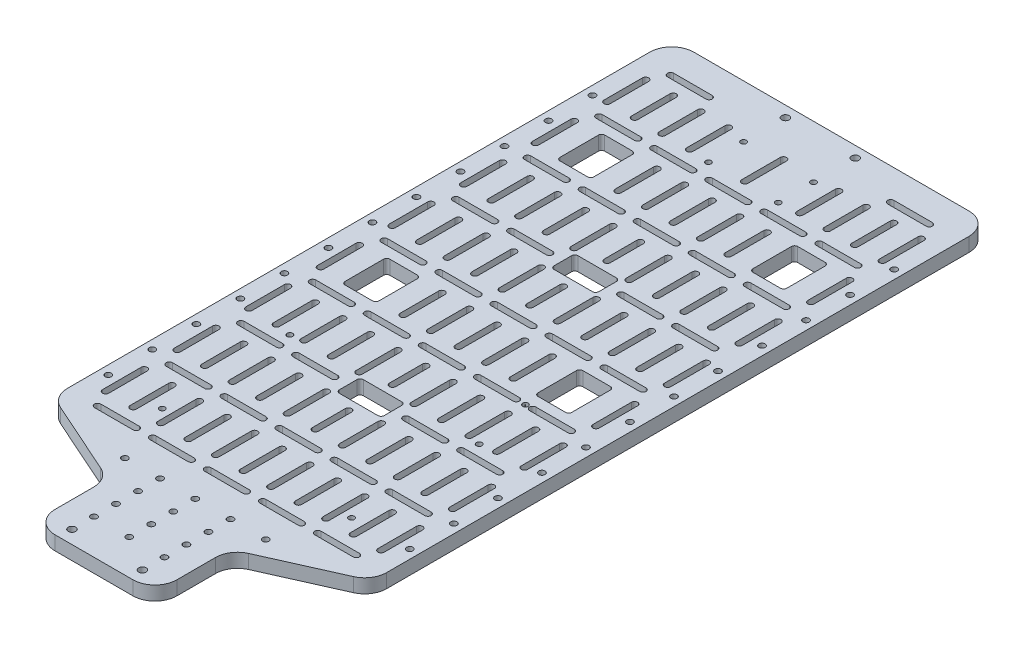
SolidWorks part; units mm, degrees
ref_plane "Front Plane" through (0, 0, 0) normal (0, 0, 1) x (1, 0, 0)
ref_plane "Top Plane" through (0, 0, 0) normal (0, 1, 0) x (1, 0, 0)
ref_plane "Right Plane" through (0, 0, 0) normal (1, 0, 0) x (0, 0, -1)
sketch "Sketch1" plane through (0, 0, 0) normal (0, 1, 0) x (1, 0, 0)
  line L0 (-72.5, 0) -> (72.5, 0)
  line L1 (-72.5, 0) -> (-72.5, -335)
  line L2 (72.5, 0) -> (72.5, -335)
  line L3 (72.5, -335) -> (-72.5, -335)
  line L4 (0, 0) -> (0, -335) construction
  dimension "D1" = 145
  dimension "D2" = 335
extrude "Boss-Extrude1" add sketch "Sketch1" along normal blind 6.35
sketch "Sketch2" plane through (0, 6.35, 0) normal (0, 1, 0) x (1, 0, 0)
  line L0 (72.5, 0) -> (-72.5, 0) construction
  line L1 (-72.5, -335) -> (72.5, -335) construction
  line L2 (0, 0) -> (0, -335) construction
  line L3 (-27.685, -301) -> (-72.5, -281)
  line L4 (16.25, -273.1552) -> (33.75, -273.1552)
  line L5 (-27.685, -335) -> (-27.685, -301)
  line L6 (-72.5, 0) -> (-72.5, -335) construction
  line L7 (-72.5, -281) -> (-72.5, -335)
  line L8 (-72.5, -335) -> (-27.685, -335)
  line L9 (-8.75, -273.1552) -> (8.75, -273.1552)
  line L10 (8.75, -276) -> (-8.75, -276)
  line L11 (33.75, -276) -> (16.25, -276)
  line L12 (41.25, -273.1552) -> (58.75, -273.1552)
  line L13 (58.75, -276) -> (41.25, -276)
  line L14 (-33.75, -273.1552) -> (-16.25, -273.1552)
  line L15 (-16.25, -276) -> (-33.75, -276)
  line L16 (-58.75, -273.1552) -> (-41.25, -273.1552)
  line L17 (-41.25, -276) -> (-58.75, -276)
  line L20 (-1.4224, -249.5776) -> (-1.4224, -267.0776)
  line L21 (1.4224, -249.5776) -> (1.4224, -267.0776)
  line L22 (13.9224, -249.5776) -> (13.9224, -267.0776)
  line L23 (11.0776, -249.5776) -> (11.0776, -267.0776)
  line L24 (26.4224, -249.5776) -> (26.4224, -267.0776)
  line L25 (23.5776, -249.5776) -> (23.5776, -267.0776)
  line L26 (38.9224, -249.5776) -> (38.9224, -267.0776)
  line L27 (36.0776, -249.5776) -> (36.0776, -267.0776)
  line L28 (51.4224, -249.5776) -> (51.4224, -267.0776)
  line L29 (48.5776, -249.5776) -> (48.5776, -267.0776)
  line L30 (63.9224, -249.5776) -> (63.9224, -267.0776)
  line L31 (61.0776, -249.5776) -> (61.0776, -267.0776)
  line L32 (-11.1007, -249.5776) -> (-11.1007, -267.0776)
  line L33 (-13.9455, -249.5776) -> (-13.9455, -267.0776)
  line L34 (-23.6238, -249.5776) -> (-23.6238, -267.0776)
  line L35 (-26.4686, -249.5776) -> (-26.4686, -267.0776)
  line L36 (-36.1468, -249.5776) -> (-36.1468, -267.0776)
  line L37 (-38.9916, -249.5776) -> (-38.9916, -267.0776)
  line L38 (-48.6699, -249.5776) -> (-48.6699, -267.0776)
  line L39 (-51.5147, -249.5776) -> (-51.5147, -267.0776)
  line L40 (-61.193, -249.5776) -> (-61.193, -267.0776)
  line L41 (-64.0378, -249.5776) -> (-64.0378, -267.0776)
  line L42 (-58.75, -240.6065) -> (-41.25, -240.6065)
  line L43 (-41.25, -243.4513) -> (-58.75, -243.4513)
  line L44 (-61.193, -217.0289) -> (-61.193, -234.5289)
  line L45 (-64.0378, -217.0289) -> (-64.0378, -234.5289)
  line L46 (-48.6699, -217.0289) -> (-48.6699, -234.5289)
  line L47 (-51.5147, -217.0289) -> (-51.5147, -234.5289)
  line L48 (-36.1468, -217.0289) -> (-36.1468, -234.5289)
  line L49 (-38.9916, -217.0289) -> (-38.9916, -234.5289)
  line L50 (-23.6238, -217.0289) -> (-23.6238, -234.5289)
  line L51 (-26.4686, -217.0289) -> (-26.4686, -234.5289)
  line L52 (-11.1007, -217.0289) -> (-11.1007, -234.5289)
  line L53 (-13.9455, -217.0289) -> (-13.9455, -234.5289)
  line L54 (-33.75, -240.6065) -> (-16.25, -240.6065)
  line L55 (-16.25, -243.4513) -> (-33.75, -243.4513)
  line L58 (13.9224, -217.0289) -> (13.9224, -234.5289)
  line L59 (11.0776, -217.0289) -> (11.0776, -234.5289)
  line L60 (26.4224, -217.0289) -> (26.4224, -234.5289)
  line L61 (23.5776, -217.0289) -> (23.5776, -234.5289)
  line L62 (16.25, -240.6065) -> (33.75, -240.6065)
  line L63 (33.75, -243.4513) -> (16.25, -243.4513)
  line L64 (-8.75, -240.6065) -> (8.75, -240.6065)
  line L65 (8.75, -243.4513) -> (-8.75, -243.4513)
  line L66 (38.9224, -217.0289) -> (38.9224, -234.5289)
  line L67 (36.0776, -217.0289) -> (36.0776, -234.5289)
  line L68 (51.4224, -217.0289) -> (51.4224, -234.5289)
  line L69 (48.5776, -217.0289) -> (48.5776, -234.5289)
  line L70 (41.25, -240.6065) -> (58.75, -240.6065)
  line L71 (58.75, -243.4513) -> (41.25, -243.4513)
  line L72 (63.9224, -217.0289) -> (63.9224, -234.5289)
  line L73 (61.0776, -217.0289) -> (61.0776, -234.5289)
  line L74 (-58.75, -208.0578) -> (-41.25, -208.0578)
  line L75 (-41.25, -210.9026) -> (-58.75, -210.9026)
  line L76 (-61.193, -184.4802) -> (-61.193, -201.9802)
  line L77 (-64.0378, -184.4802) -> (-64.0378, -201.9802)
  line L78 (-48.6699, -184.4802) -> (-48.6699, -201.9802)
  line L79 (-51.5147, -184.4802) -> (-51.5147, -201.9802)
  line L80 (-36.1468, -184.4802) -> (-36.1468, -201.9802)
  line L81 (-38.9916, -184.4802) -> (-38.9916, -201.9802)
  line L82 (-23.6238, -184.4802) -> (-23.6238, -201.9802)
  line L83 (-26.4686, -184.4802) -> (-26.4686, -201.9802)
  line L84 (-11.1007, -184.4802) -> (-11.1007, -201.9802)
  line L85 (-13.9455, -184.4802) -> (-13.9455, -201.9802)
  line L86 (-33.75, -208.0578) -> (-16.25, -208.0578)
  line L87 (-16.25, -210.9026) -> (-33.75, -210.9026)
  line L90 (13.9224, -184.4802) -> (13.9224, -201.9802)
  line L91 (11.0776, -184.4802) -> (11.0776, -201.9802)
  line L92 (26.4224, -184.4802) -> (26.4224, -201.9802)
  line L93 (23.5776, -184.4802) -> (23.5776, -201.9802)
  line L94 (16.25, -208.0578) -> (33.75, -208.0578)
  line L95 (33.75, -210.9026) -> (16.25, -210.9026)
  line L98 (38.9224, -184.4802) -> (38.9224, -201.9802)
  line L99 (36.0776, -184.4802) -> (36.0776, -201.9802)
  line L100 (51.4224, -184.4802) -> (51.4224, -201.9802)
  line L101 (48.5776, -184.4802) -> (48.5776, -201.9802)
  line L102 (41.25, -208.0578) -> (58.75, -208.0578)
  line L103 (58.75, -210.9026) -> (41.25, -210.9026)
  line L104 (63.9224, -184.4802) -> (63.9224, -201.9802)
  line L105 (61.0776, -184.4802) -> (61.0776, -201.9802)
  line L106 (-58.75, -175.509) -> (-41.25, -175.509)
  line L107 (-41.25, -178.3538) -> (-58.75, -178.3538)
  line L108 (-61.193, -151.9314) -> (-61.193, -169.4314)
  line L109 (-64.0378, -151.9314) -> (-64.0378, -169.4314)
  line L111 (-51.5147, -151.9314) -> (-51.5147, -169.4314)
  line L112 (-36.1468, -151.9314) -> (-36.1468, -169.4314)
  line L114 (-23.6238, -151.9314) -> (-23.6238, -169.4314)
  line L115 (-26.4686, -151.9314) -> (-26.4686, -169.4314)
  line L116 (-11.1007, -151.9314) -> (-11.1007, -169.4314)
  line L117 (-13.9455, -151.9314) -> (-13.9455, -169.4314)
  line L118 (-33.75, -175.509) -> (-16.25, -175.509)
  line L119 (-16.25, -178.3538) -> (-33.75, -178.3538)
  line L120 (1.4224, -151.9314) -> (1.4224, -169.4314)
  line L121 (-1.4224, -151.9314) -> (-1.4224, -169.4314)
  line L122 (13.9224, -151.9314) -> (13.9224, -169.4314)
  line L123 (11.0776, -151.9314) -> (11.0776, -169.4314)
  line L124 (26.4224, -151.9314) -> (26.4224, -169.4314)
  line L125 (23.5776, -151.9314) -> (23.5776, -169.4314)
  line L126 (16.25, -175.509) -> (33.75, -175.509)
  line L127 (33.75, -178.3538) -> (16.25, -178.3538)
  line L128 (-8.75, -175.509) -> (8.75, -175.509)
  line L129 (8.75, -178.3538) -> (-8.75, -178.3538)
  line L134 (41.25, -175.509) -> (58.75, -175.509)
  line L135 (58.75, -178.3538) -> (41.25, -178.3538)
  line L136 (63.9224, -151.9314) -> (63.9224, -169.4314)
  line L137 (61.0776, -151.9314) -> (61.0776, -169.4314)
  line L138 (-58.75, -142.9603) -> (-41.25, -142.9603)
  line L139 (-41.25, -145.8051) -> (-58.75, -145.8051)
  line L140 (-61.193, -119.3827) -> (-61.193, -136.8827)
  line L141 (-64.0378, -119.3827) -> (-64.0378, -136.8827)
  line L142 (-48.6699, -119.3827) -> (-48.6699, -136.8827)
  line L143 (-51.5147, -119.3827) -> (-51.5147, -136.8827)
  line L144 (-36.1468, -119.3827) -> (-36.1468, -136.8827)
  line L145 (-38.9916, -119.3827) -> (-38.9916, -136.8827)
  line L146 (-23.6238, -119.3827) -> (-23.6238, -136.8827)
  line L147 (-26.4686, -119.3827) -> (-26.4686, -136.8827)
  line L148 (-11.1007, -119.3827) -> (-11.1007, -136.8827)
  line L149 (-13.9455, -119.3827) -> (-13.9455, -136.8827)
  line L150 (-33.75, -142.9603) -> (-16.25, -142.9603)
  line L151 (-16.25, -145.8051) -> (-33.75, -145.8051)
  line L154 (13.9224, -119.3827) -> (13.9224, -136.8827)
  line L155 (11.0776, -119.3827) -> (11.0776, -136.8827)
  line L156 (26.4224, -119.3827) -> (26.4224, -136.8827)
  line L157 (23.5776, -119.3827) -> (23.5776, -136.8827)
  line L158 (16.25, -142.9603) -> (33.75, -142.9603)
  line L159 (33.75, -145.8051) -> (16.25, -145.8051)
  line L160 (-8.75, -142.9603) -> (8.75, -142.9603)
  line L161 (8.75, -145.8051) -> (-8.75, -145.8051)
  line L162 (38.9224, -119.3827) -> (38.9224, -136.8827)
  line L163 (36.0776, -119.3827) -> (36.0776, -136.8827)
  line L164 (51.4224, -119.3827) -> (51.4224, -136.8827)
  line L165 (48.5776, -119.3827) -> (48.5776, -136.8827)
  line L166 (41.25, -142.9603) -> (58.75, -142.9603)
  line L167 (58.75, -145.8051) -> (41.25, -145.8051)
  line L168 (63.9224, -119.3827) -> (63.9224, -136.8827)
  line L169 (61.0776, -119.3827) -> (61.0776, -136.8827)
  line L170 (-58.75, -110.4116) -> (-41.25, -110.4116)
  line L171 (-41.25, -113.2564) -> (-58.75, -113.2564)
  line L172 (-61.193, -86.834) -> (-61.193, -104.334)
  line L173 (-64.0378, -86.834) -> (-64.0378, -104.334)
  line L174 (-48.6699, -86.834) -> (-48.6699, -104.334)
  line L175 (-51.5147, -86.834) -> (-51.5147, -104.334)
  line L176 (-36.1468, -86.834) -> (-36.1468, -104.334)
  line L177 (-38.9916, -86.834) -> (-38.9916, -104.334)
  line L178 (-23.6238, -86.834) -> (-23.6238, -104.334)
  line L179 (-26.4686, -86.834) -> (-26.4686, -104.334)
  line L180 (-11.1007, -86.834) -> (-11.1007, -104.334)
  line L181 (-13.9455, -86.834) -> (-13.9455, -104.334)
  line L182 (-33.75, -110.4116) -> (-16.25, -110.4116)
  line L183 (-16.25, -113.2564) -> (-33.75, -113.2564)
  line L186 (13.9224, -86.834) -> (13.9224, -104.334)
  line L187 (11.0776, -86.834) -> (11.0776, -104.334)
  line L188 (26.4224, -86.834) -> (26.4224, -104.334)
  line L189 (23.5776, -86.834) -> (23.5776, -104.334)
  line L190 (16.25, -110.4116) -> (33.75, -110.4116)
  line L191 (33.75, -113.2564) -> (16.25, -113.2564)
  line L194 (38.9224, -86.834) -> (38.9224, -104.334)
  line L195 (36.0776, -86.834) -> (36.0776, -104.334)
  line L196 (51.4224, -86.834) -> (51.4224, -104.334)
  line L197 (48.5776, -86.834) -> (48.5776, -104.334)
  line L198 (41.25, -110.4116) -> (58.75, -110.4116)
  line L199 (58.75, -113.2564) -> (41.25, -113.2564)
  line L200 (63.9224, -86.834) -> (63.9224, -104.334)
  line L201 (61.0776, -86.834) -> (61.0776, -104.334)
  line L202 (-58.75, -77.8629) -> (-41.25, -77.8629)
  line L203 (-41.25, -80.7077) -> (-58.75, -80.7077)
  line L204 (-61.193, -54.2853) -> (-61.193, -71.7853)
  line L205 (-64.0378, -54.2853) -> (-64.0378, -71.7853)
  line L207 (-51.5147, -54.2853) -> (-51.5147, -71.7853)
  line L208 (-36.1468, -54.2853) -> (-36.1468, -71.7853)
  line L210 (-23.6238, -54.2853) -> (-23.6238, -71.7853)
  line L211 (-26.4686, -54.2853) -> (-26.4686, -71.7853)
  line L212 (-11.1007, -54.2853) -> (-11.1007, -71.7853)
  line L213 (-13.9455, -54.2853) -> (-13.9455, -71.7853)
  line L214 (-33.75, -77.8629) -> (-16.25, -77.8629)
  line L215 (-16.25, -80.7077) -> (-33.75, -80.7077)
  line L216 (1.4224, -54.2853) -> (1.4224, -71.7853)
  line L217 (-1.4224, -54.2853) -> (-1.4224, -71.7853)
  line L218 (13.9224, -54.2853) -> (13.9224, -71.7853)
  line L219 (11.0776, -54.2853) -> (11.0776, -71.7853)
  line L220 (26.4224, -54.2853) -> (26.4224, -71.7853)
  line L221 (23.5776, -54.2853) -> (23.5776, -71.7853)
  line L222 (16.25, -77.8629) -> (33.75, -77.8629)
  line L223 (33.75, -80.7077) -> (16.25, -80.7077)
  line L224 (-8.75, -77.8629) -> (8.75, -77.8629)
  line L225 (8.75, -80.7077) -> (-8.75, -80.7077)
  line L230 (41.25, -77.8629) -> (58.75, -77.8629)
  line L231 (58.75, -80.7077) -> (41.25, -80.7077)
  line L232 (63.9224, -54.2853) -> (63.9224, -71.7853)
  line L233 (61.0776, -54.2853) -> (61.0776, -71.7853)
  line L234 (-41.25, -48.2077) -> (-58.75, -48.2077)
  line L235 (-58.75, -45.3629) -> (-41.25, -45.3629)
  line L236 (-33.75, -45.3629) -> (-16.25, -45.3629)
  line L237 (-16.25, -48.2077) -> (-33.75, -48.2077)
  line L238 (-8.75, -45.3629) -> (8.75, -45.3629)
  line L239 (8.75, -48.2077) -> (-8.75, -48.2077)
  line L240 (16.25, -45.3629) -> (33.75, -45.3629)
  line L241 (33.75, -48.2077) -> (16.25, -48.2077)
  line L242 (41.25, -45.3629) -> (58.75, -45.3629)
  line L243 (58.75, -48.2077) -> (41.25, -48.2077)
  line L244 (72.5, -281) -> (72.5, -335)
  line L245 (27.685, -301) -> (72.5, -281)
  line L246 (27.685, -335) -> (27.685, -301)
  line L247 (72.5, -335) -> (27.685, -335)
  line L248 (-48.6699, -21.7853) -> (-48.6699, -39.2853)
  line L249 (-51.5147, -21.7853) -> (-51.5147, -39.2853)
  line L250 (-36.1468, -21.7853) -> (-36.1468, -39.2853)
  line L251 (-38.9916, -21.7853) -> (-38.9916, -39.2853)
  line L252 (51.4224, -21.7853) -> (51.4224, -39.2853)
  line L253 (48.5776, -21.7853) -> (48.5776, -39.2853)
  line L254 (38.9224, -21.7853) -> (38.9224, -39.2853)
  line L255 (36.0776, -21.7853) -> (36.0776, -39.2853)
  line L256 (63.9224, -21.7853) -> (63.9224, -39.2853)
  line L257 (61.0776, -21.7853) -> (61.0776, -39.2853)
  line L258 (-61.193, -21.7853) -> (-61.193, -39.2853)
  line L259 (-64.0378, -21.7853) -> (-64.0378, -39.2853)
  line L260 (-23.6238, -21.7853) -> (-23.6238, -39.2853)
  line L261 (-26.4686, -21.7853) -> (-26.4686, -39.2853)
  line L262 (26.4224, -21.7853) -> (26.4224, -39.2853)
  line L263 (23.5776, -21.7853) -> (23.5776, -39.2853)
  line L264 (1.4224, -21.7853) -> (1.4224, -39.2853)
  line L265 (-1.4224, -21.7853) -> (-1.4224, -39.2853)
  line L266 (-41.25, -15.7077) -> (-58.75, -15.7077)
  line L267 (-58.75, -12.8629) -> (-41.25, -12.8629)
  line L268 (41.25, -12.8629) -> (58.75, -12.8629)
  line L269 (58.75, -15.7077) -> (41.25, -15.7077)
  line L270 (-50.0923, -150.509) -> (-37.5692, -150.509)
  line L271 (-50.0923, -170.8538) -> (-37.5692, -170.8538)
  line L272 (-50.0923, -52.8629) -> (-37.5692, -52.8629)
  line L273 (-48.6699, -151.9314) -> (-48.6699, -169.4314) [skipped]
  line L274 (-38.9916, -151.9314) -> (-38.9916, -169.4314) [skipped]
  line L275 (38.9224, -151.9314) -> (38.9224, -169.4314) [skipped]
  line L276 (36.0776, -151.9314) -> (36.0776, -169.4314) [skipped]
  line L277 (51.4224, -151.9314) -> (51.4224, -169.4314) [skipped]
  line L278 (48.5776, -151.9314) -> (48.5776, -169.4314) [skipped]
  line L279 (-50.0923, -73.2077) -> (-37.5692, -73.2077)
  line L281 (-48.6699, -54.2853) -> (-48.6699, -71.7853) [skipped]
  line L282 (-38.9916, -54.2853) -> (-38.9916, -71.7853) [skipped]
  line L283 (38.9224, -54.2853) -> (38.9224, -71.7853) [skipped]
  line L284 (36.0776, -54.2853) -> (36.0776, -71.7853) [skipped]
  line L285 (51.4224, -54.2853) -> (51.4224, -71.7853) [skipped]
  line L286 (48.5776, -54.2853) -> (48.5776, -71.7853) [skipped]
  line L287 (8.75, -117.2564) -> (-8.75, -117.2564)
  line L288 (-8.75, -106.4116) -> (8.75, -106.4116)
  line L290 (-10.1724, -107.834) -> (-10.1724, -115.834)
  line L291 (10.1724, -107.834) -> (10.1724, -115.834)
  line L292 (8.75, -113.2564) -> (0, -113.2564) [skipped]
  line L293 (0, -110.4116) -> (8.75, -110.4116) [skipped]
  line L294 (1.4224, -86.8342) -> (1.42, -101.8342)
  line L295 (-1.4224, -86.8342) -> (-1.42, -101.8342)
  line L296 (1.4224, -86.834) -> (1.4224, -104.334) [skipped]
  line L297 (-1.4224, -86.834) -> (-1.4224, -104.334) [skipped]
  line L298 (1.4224, -121.8829) -> (1.42, -136.8829)
  line L299 (-1.4224, -121.8829) -> (-1.42, -136.8829)
  line L300 (1.4224, -119.3827) -> (1.4224, -136.8827) [skipped]
  line L301 (-1.4224, -119.3827) -> (-1.4224, -136.8827) [skipped]
  line L302 (8.75, -214.7564) -> (-8.75, -214.7564)
  line L303 (10.1724, -205.334) -> (10.1724, -213.334)
  line L304 (-8.75, -203.9116) -> (8.75, -203.9116)
  line L305 (-10.1724, -205.334) -> (-10.1724, -213.334)
  line L306 (1.4224, -184.3342) -> (1.42, -199.3342)
  line L307 (-1.4224, -184.3342) -> (-1.42, -199.3342)
  line L308 (1.4224, -219.3829) -> (1.42, -234.3829)
  line L309 (-1.4224, -219.3829) -> (-1.42, -234.3829)
  line L310 (1.4224, -184.4802) -> (1.4224, -201.9802) [skipped]
  line L311 (-1.4224, -184.4802) -> (-1.4224, -201.9802) [skipped]
  line L312 (-8.75, -208.0578) -> (8.75, -208.0578) [skipped]
  line L313 (8.75, -210.9026) -> (-8.75, -210.9026) [skipped]
  line L314 (1.4224, -217.0289) -> (1.4224, -234.5289) [skipped]
  line L315 (-1.4224, -217.0289) -> (-1.4224, -234.5289) [skipped]
  line L316 (50.0923, -52.8629) -> (37.5692, -52.8629)
  line L317 (36.1468, -54.2853) -> (36.1468, -71.7853)
  line L318 (50.0923, -73.2077) -> (37.5692, -73.2077)
  line L319 (51.5147, -54.2853) -> (51.5147, -71.7853)
  line L320 (50.0923, -150.509) -> (37.5692, -150.509)
  line L321 (36.1468, -151.9314) -> (36.1468, -169.4314)
  line L322 (50.0923, -170.8538) -> (37.5692, -170.8538)
  line L323 (51.5147, -151.9314) -> (51.5147, -169.4314)
  circle A0 centre (-15.875, -5) radius 1.7
  circle A1 centre (-16, -329) radius 1.7
  arc A2 (8.75, -276) -> (8.75, -273.1552) centre (8.75, -274.5776) ccw
  arc A3 (-8.75, -273.1552) -> (-8.75, -276) centre (-8.75, -274.5776) ccw
  arc A4 (33.75, -276) -> (33.75, -273.1552) centre (33.75, -274.5776) ccw
  arc A5 (16.25, -273.1552) -> (16.25, -276) centre (16.25, -274.5776) ccw
  arc A6 (58.75, -276) -> (58.75, -273.1552) centre (58.75, -274.5776) ccw
  arc A7 (41.25, -273.1552) -> (41.25, -276) centre (41.25, -274.5776) ccw
  arc A8 (-16.25, -276) -> (-16.25, -273.1552) centre (-16.25, -274.5776) ccw
  arc A9 (-33.75, -273.1552) -> (-33.75, -276) centre (-33.75, -274.5776) ccw
  arc A10 (-41.25, -276) -> (-41.25, -273.1552) centre (-41.25, -274.5776) ccw
  arc A11 (-58.75, -273.1552) -> (-58.75, -276) centre (-58.75, -274.5776) ccw
  arc A14 (1.4224, -249.5776) -> (-1.4224, -249.5776) centre (0, -249.5776) ccw
  arc A15 (-1.4224, -267.0776) -> (1.4224, -267.0776) centre (0, -267.0776) ccw
  arc A16 (11.0776, -267.0776) -> (13.9224, -267.0776) centre (12.5, -267.0776) ccw
  arc A17 (13.9224, -249.5776) -> (11.0776, -249.5776) centre (12.5, -249.5776) ccw
  arc A18 (23.5776, -267.0776) -> (26.4224, -267.0776) centre (25, -267.0776) ccw
  arc A19 (26.4224, -249.5776) -> (23.5776, -249.5776) centre (25, -249.5776) ccw
  arc A20 (36.0776, -267.0776) -> (38.9224, -267.0776) centre (37.5, -267.0776) ccw
  arc A21 (38.9224, -249.5776) -> (36.0776, -249.5776) centre (37.5, -249.5776) ccw
  arc A22 (48.5776, -267.0776) -> (51.4224, -267.0776) centre (50, -267.0776) ccw
  arc A23 (51.4224, -249.5776) -> (48.5776, -249.5776) centre (50, -249.5776) ccw
  arc A24 (61.0776, -267.0776) -> (63.9224, -267.0776) centre (62.5, -267.0776) ccw
  arc A25 (63.9224, -249.5776) -> (61.0776, -249.5776) centre (62.5, -249.5776) ccw
  arc A26 (-13.9455, -267.0776) -> (-11.1007, -267.0776) centre (-12.5231, -267.0776) ccw
  arc A27 (-11.1007, -249.5776) -> (-13.9455, -249.5776) centre (-12.5231, -249.5776) ccw
  arc A28 (-26.4686, -267.0776) -> (-23.6238, -267.0776) centre (-25.0462, -267.0776) ccw
  arc A29 (-23.6238, -249.5776) -> (-26.4686, -249.5776) centre (-25.0462, -249.5776) ccw
  arc A30 (-38.9916, -267.0776) -> (-36.1468, -267.0776) centre (-37.5692, -267.0776) ccw
  arc A31 (-36.1468, -249.5776) -> (-38.9916, -249.5776) centre (-37.5692, -249.5776) ccw
  arc A32 (-51.5147, -267.0776) -> (-48.6699, -267.0776) centre (-50.0923, -267.0776) ccw
  arc A33 (-48.6699, -249.5776) -> (-51.5147, -249.5776) centre (-50.0923, -249.5776) ccw
  arc A34 (-64.0378, -267.0776) -> (-61.193, -267.0776) centre (-62.6154, -267.0776) ccw
  arc A35 (-61.193, -249.5776) -> (-64.0378, -249.5776) centre (-62.6154, -249.5776) ccw
  arc A36 (-41.25, -243.4513) -> (-41.25, -240.6065) centre (-41.25, -242.0289) ccw
  arc A37 (-58.75, -240.6065) -> (-58.75, -243.4513) centre (-58.75, -242.0289) ccw
  arc A38 (-64.0378, -234.5289) -> (-61.193, -234.5289) centre (-62.6154, -234.5289) ccw
  arc A39 (-61.193, -217.0289) -> (-64.0378, -217.0289) centre (-62.6154, -217.0289) ccw
  arc A40 (-51.5147, -234.5289) -> (-48.6699, -234.5289) centre (-50.0923, -234.5289) ccw
  arc A41 (-48.6699, -217.0289) -> (-51.5147, -217.0289) centre (-50.0923, -217.0289) ccw
  arc A42 (-38.9916, -234.5289) -> (-36.1468, -234.5289) centre (-37.5692, -234.5289) ccw
  arc A43 (-36.1468, -217.0289) -> (-38.9916, -217.0289) centre (-37.5692, -217.0289) ccw
  arc A44 (-26.4686, -234.5289) -> (-23.6238, -234.5289) centre (-25.0462, -234.5289) ccw
  arc A45 (-23.6238, -217.0289) -> (-26.4686, -217.0289) centre (-25.0462, -217.0289) ccw
  arc A46 (-13.9455, -234.5289) -> (-11.1007, -234.5289) centre (-12.5231, -234.5289) ccw
  arc A47 (-11.1007, -217.0289) -> (-13.9455, -217.0289) centre (-12.5231, -217.0289) ccw
  arc A48 (-16.25, -243.4513) -> (-16.25, -240.6065) centre (-16.25, -242.0289) ccw
  arc A49 (-33.75, -240.6065) -> (-33.75, -243.4513) centre (-33.75, -242.0289) ccw
  arc A52 (11.0776, -234.5289) -> (13.9224, -234.5289) centre (12.5, -234.5289) ccw
  arc A53 (13.9224, -217.0289) -> (11.0776, -217.0289) centre (12.5, -217.0289) ccw
  arc A54 (23.5776, -234.5289) -> (26.4224, -234.5289) centre (25, -234.5289) ccw
  arc A55 (26.4224, -217.0289) -> (23.5776, -217.0289) centre (25, -217.0289) ccw
  arc A56 (33.75, -243.4513) -> (33.75, -240.6065) centre (33.75, -242.0289) ccw
  arc A57 (16.25, -240.6065) -> (16.25, -243.4513) centre (16.25, -242.0289) ccw
  arc A58 (8.75, -243.4513) -> (8.75, -240.6065) centre (8.75, -242.0289) ccw
  arc A59 (-8.75, -240.6065) -> (-8.75, -243.4513) centre (-8.75, -242.0289) ccw
  arc A60 (36.0776, -234.5289) -> (38.9224, -234.5289) centre (37.5, -234.5289) ccw
  arc A61 (38.9224, -217.0289) -> (36.0776, -217.0289) centre (37.5, -217.0289) ccw
  arc A62 (48.5776, -234.5289) -> (51.4224, -234.5289) centre (50, -234.5289) ccw
  arc A63 (51.4224, -217.0289) -> (48.5776, -217.0289) centre (50, -217.0289) ccw
  arc A64 (58.75, -243.4513) -> (58.75, -240.6065) centre (58.75, -242.0289) ccw
  arc A65 (41.25, -240.6065) -> (41.25, -243.4513) centre (41.25, -242.0289) ccw
  arc A66 (61.0776, -234.5289) -> (63.9224, -234.5289) centre (62.5, -234.5289) ccw
  arc A67 (63.9224, -217.0289) -> (61.0776, -217.0289) centre (62.5, -217.0289) ccw
  arc A68 (-41.25, -210.9026) -> (-41.25, -208.0578) centre (-41.25, -209.4802) ccw
  arc A69 (-58.75, -208.0578) -> (-58.75, -210.9026) centre (-58.75, -209.4802) ccw
  arc A70 (-64.0378, -201.9802) -> (-61.193, -201.9802) centre (-62.6154, -201.9802) ccw
  arc A71 (-61.193, -184.4802) -> (-64.0378, -184.4802) centre (-62.6154, -184.4802) ccw
  arc A72 (-51.5147, -201.9802) -> (-48.6699, -201.9802) centre (-50.0923, -201.9802) ccw
  arc A73 (-48.6699, -184.4802) -> (-51.5147, -184.4802) centre (-50.0923, -184.4802) ccw
  arc A74 (-38.9916, -201.9802) -> (-36.1468, -201.9802) centre (-37.5692, -201.9802) ccw
  arc A75 (-36.1468, -184.4802) -> (-38.9916, -184.4802) centre (-37.5692, -184.4802) ccw
  arc A76 (-26.4686, -201.9802) -> (-23.6238, -201.9802) centre (-25.0462, -201.9802) ccw
  arc A77 (-23.6238, -184.4802) -> (-26.4686, -184.4802) centre (-25.0462, -184.4802) ccw
  arc A78 (-13.9455, -201.9802) -> (-11.1007, -201.9802) centre (-12.5231, -201.9802) ccw
  arc A79 (-11.1007, -184.4802) -> (-13.9455, -184.4802) centre (-12.5231, -184.4802) ccw
  arc A80 (-16.25, -210.9026) -> (-16.25, -208.0578) centre (-16.25, -209.4802) ccw
  arc A81 (-33.75, -208.0578) -> (-33.75, -210.9026) centre (-33.75, -209.4802) ccw
  arc A84 (11.0776, -201.9802) -> (13.9224, -201.9802) centre (12.5, -201.9802) ccw
  arc A85 (13.9224, -184.4802) -> (11.0776, -184.4802) centre (12.5, -184.4802) ccw
  arc A86 (23.5776, -201.9802) -> (26.4224, -201.9802) centre (25, -201.9802) ccw
  arc A87 (26.4224, -184.4802) -> (23.5776, -184.4802) centre (25, -184.4802) ccw
  arc A88 (33.75, -210.9026) -> (33.75, -208.0578) centre (33.75, -209.4802) ccw
  arc A89 (16.25, -208.0578) -> (16.25, -210.9026) centre (16.25, -209.4802) ccw
  arc A92 (36.0776, -201.9802) -> (38.9224, -201.9802) centre (37.5, -201.9802) ccw
  arc A93 (38.9224, -184.4802) -> (36.0776, -184.4802) centre (37.5, -184.4802) ccw
  arc A94 (48.5776, -201.9802) -> (51.4224, -201.9802) centre (50, -201.9802) ccw
  arc A95 (51.4224, -184.4802) -> (48.5776, -184.4802) centre (50, -184.4802) ccw
  arc A96 (58.75, -210.9026) -> (58.75, -208.0578) centre (58.75, -209.4802) ccw
  arc A97 (41.25, -208.0578) -> (41.25, -210.9026) centre (41.25, -209.4802) ccw
  arc A98 (61.0776, -201.9802) -> (63.9224, -201.9802) centre (62.5, -201.9802) ccw
  arc A99 (63.9224, -184.4802) -> (61.0776, -184.4802) centre (62.5, -184.4802) ccw
  arc A100 (-41.25, -178.3538) -> (-41.25, -175.509) centre (-41.25, -176.9314) ccw
  arc A101 (-58.75, -175.509) -> (-58.75, -178.3538) centre (-58.75, -176.9314) ccw
  arc A102 (-64.0378, -169.4314) -> (-61.193, -169.4314) centre (-62.6154, -169.4314) ccw
  arc A103 (-61.193, -151.9314) -> (-64.0378, -151.9314) centre (-62.6154, -151.9314) ccw
  arc A104 (-51.5147, -169.4314) -> (-50.0923, -170.8538) centre (-50.0923, -169.4314) ccw
  arc A105 (-50.0923, -150.509) -> (-51.5147, -151.9314) centre (-50.0923, -151.9314) ccw
  arc A106 (-37.5692, -170.8538) -> (-36.1468, -169.4314) centre (-37.5692, -169.4314) ccw
  arc A107 (-36.1468, -151.9314) -> (-37.5692, -150.509) centre (-37.5692, -151.9314) ccw
  arc A108 (-26.4686, -169.4314) -> (-23.6238, -169.4314) centre (-25.0462, -169.4314) ccw
  arc A109 (-23.6238, -151.9314) -> (-26.4686, -151.9314) centre (-25.0462, -151.9314) ccw
  arc A110 (-13.9455, -169.4314) -> (-11.1007, -169.4314) centre (-12.5231, -169.4314) ccw
  arc A111 (-11.1007, -151.9314) -> (-13.9455, -151.9314) centre (-12.5231, -151.9314) ccw
  arc A112 (-16.25, -178.3538) -> (-16.25, -175.509) centre (-16.25, -176.9314) ccw
  arc A113 (-33.75, -175.509) -> (-33.75, -178.3538) centre (-33.75, -176.9314) ccw
  arc A114 (-1.4224, -169.4314) -> (1.4224, -169.4314) centre (0, -169.4314) ccw
  arc A115 (1.4224, -151.9314) -> (-1.4224, -151.9314) centre (0, -151.9314) ccw
  arc A116 (11.0776, -169.4314) -> (13.9224, -169.4314) centre (12.5, -169.4314) ccw
  arc A117 (13.9224, -151.9314) -> (11.0776, -151.9314) centre (12.5, -151.9314) ccw
  arc A118 (23.5776, -169.4314) -> (26.4224, -169.4314) centre (25, -169.4314) ccw
  arc A119 (26.4224, -151.9314) -> (23.5776, -151.9314) centre (25, -151.9314) ccw
  arc A120 (33.75, -178.3538) -> (33.75, -175.509) centre (33.75, -176.9314) ccw
  arc A121 (16.25, -175.509) -> (16.25, -178.3538) centre (16.25, -176.9314) ccw
  arc A122 (8.75, -178.3538) -> (8.75, -175.509) centre (8.75, -176.9314) ccw
  arc A123 (-8.75, -175.509) -> (-8.75, -178.3538) centre (-8.75, -176.9314) ccw
  arc A128 (58.75, -178.3538) -> (58.75, -175.509) centre (58.75, -176.9314) ccw
  arc A129 (41.25, -175.509) -> (41.25, -178.3538) centre (41.25, -176.9314) ccw
  arc A130 (61.0776, -169.4314) -> (63.9224, -169.4314) centre (62.5, -169.4314) ccw
  arc A131 (63.9224, -151.9314) -> (61.0776, -151.9314) centre (62.5, -151.9314) ccw
  arc A132 (-41.25, -145.8051) -> (-41.25, -142.9603) centre (-41.25, -144.3827) ccw
  arc A133 (-58.75, -142.9603) -> (-58.75, -145.8051) centre (-58.75, -144.3827) ccw
  arc A134 (-64.0378, -136.8827) -> (-61.193, -136.8827) centre (-62.6154, -136.8827) ccw
  arc A135 (-61.193, -119.3827) -> (-64.0378, -119.3827) centre (-62.6154, -119.3827) ccw
  arc A136 (-51.5147, -136.8827) -> (-48.6699, -136.8827) centre (-50.0923, -136.8827) ccw
  arc A137 (-48.6699, -119.3827) -> (-51.5147, -119.3827) centre (-50.0923, -119.3827) ccw
  arc A138 (-38.9916, -136.8827) -> (-36.1468, -136.8827) centre (-37.5692, -136.8827) ccw
  arc A139 (-36.1468, -119.3827) -> (-38.9916, -119.3827) centre (-37.5692, -119.3827) ccw
  arc A140 (-26.4686, -136.8827) -> (-23.6238, -136.8827) centre (-25.0462, -136.8827) ccw
  arc A141 (-23.6238, -119.3827) -> (-26.4686, -119.3827) centre (-25.0462, -119.3827) ccw
  arc A142 (-13.9455, -136.8827) -> (-11.1007, -136.8827) centre (-12.5231, -136.8827) ccw
  arc A143 (-11.1007, -119.3827) -> (-13.9455, -119.3827) centre (-12.5231, -119.3827) ccw
  arc A144 (-16.25, -145.8051) -> (-16.25, -142.9603) centre (-16.25, -144.3827) ccw
  arc A145 (-33.75, -142.9603) -> (-33.75, -145.8051) centre (-33.75, -144.3827) ccw
  arc A148 (11.0776, -136.8827) -> (13.9224, -136.8827) centre (12.5, -136.8827) ccw
  arc A149 (13.9224, -119.3827) -> (11.0776, -119.3827) centre (12.5, -119.3827) ccw
  arc A150 (23.5776, -136.8827) -> (26.4224, -136.8827) centre (25, -136.8827) ccw
  arc A151 (26.4224, -119.3827) -> (23.5776, -119.3827) centre (25, -119.3827) ccw
  arc A152 (33.75, -145.8051) -> (33.75, -142.9603) centre (33.75, -144.3827) ccw
  arc A153 (16.25, -142.9603) -> (16.25, -145.8051) centre (16.25, -144.3827) ccw
  arc A154 (8.75, -145.8051) -> (8.75, -142.9603) centre (8.75, -144.3827) ccw
  arc A155 (-8.75, -142.9603) -> (-8.75, -145.8051) centre (-8.75, -144.3827) ccw
  arc A156 (36.0776, -136.8827) -> (38.9224, -136.8827) centre (37.5, -136.8827) ccw
  arc A157 (38.9224, -119.3827) -> (36.0776, -119.3827) centre (37.5, -119.3827) ccw
  arc A158 (48.5776, -136.8827) -> (51.4224, -136.8827) centre (50, -136.8827) ccw
  arc A159 (51.4224, -119.3827) -> (48.5776, -119.3827) centre (50, -119.3827) ccw
  arc A160 (58.75, -145.8051) -> (58.75, -142.9603) centre (58.75, -144.3827) ccw
  arc A161 (41.25, -142.9603) -> (41.25, -145.8051) centre (41.25, -144.3827) ccw
  arc A162 (61.0776, -136.8827) -> (63.9224, -136.8827) centre (62.5, -136.8827) ccw
  arc A163 (63.9224, -119.3827) -> (61.0776, -119.3827) centre (62.5, -119.3827) ccw
  arc A164 (-41.25, -113.2564) -> (-41.25, -110.4116) centre (-41.25, -111.834) ccw
  arc A165 (-58.75, -110.4116) -> (-58.75, -113.2564) centre (-58.75, -111.834) ccw
  arc A166 (-64.0378, -104.334) -> (-61.193, -104.334) centre (-62.6154, -104.334) ccw
  arc A167 (-61.193, -86.834) -> (-64.0378, -86.834) centre (-62.6154, -86.834) ccw
  arc A168 (-51.5147, -104.334) -> (-48.6699, -104.334) centre (-50.0923, -104.334) ccw
  arc A169 (-48.6699, -86.834) -> (-51.5147, -86.834) centre (-50.0923, -86.834) ccw
  arc A170 (-38.9916, -104.334) -> (-36.1468, -104.334) centre (-37.5692, -104.334) ccw
  arc A171 (-36.1468, -86.834) -> (-38.9916, -86.834) centre (-37.5692, -86.834) ccw
  arc A172 (-26.4686, -104.334) -> (-23.6238, -104.334) centre (-25.0462, -104.334) ccw
  arc A173 (-23.6238, -86.834) -> (-26.4686, -86.834) centre (-25.0462, -86.834) ccw
  arc A174 (-13.9455, -104.334) -> (-11.1007, -104.334) centre (-12.5231, -104.334) ccw
  arc A175 (-11.1007, -86.834) -> (-13.9455, -86.834) centre (-12.5231, -86.834) ccw
  arc A176 (-16.25, -113.2564) -> (-16.25, -110.4116) centre (-16.25, -111.834) ccw
  arc A177 (-33.75, -110.4116) -> (-33.75, -113.2564) centre (-33.75, -111.834) ccw
  arc A180 (11.0776, -104.334) -> (13.9224, -104.334) centre (12.5, -104.334) ccw
  arc A181 (13.9224, -86.834) -> (11.0776, -86.834) centre (12.5, -86.834) ccw
  arc A182 (23.5776, -104.334) -> (26.4224, -104.334) centre (25, -104.334) ccw
  arc A183 (26.4224, -86.834) -> (23.5776, -86.834) centre (25, -86.834) ccw
  arc A184 (33.75, -113.2564) -> (33.75, -110.4116) centre (33.75, -111.834) ccw
  arc A185 (16.25, -110.4116) -> (16.25, -113.2564) centre (16.25, -111.834) ccw
  arc A188 (36.0776, -104.334) -> (38.9224, -104.334) centre (37.5, -104.334) ccw
  arc A189 (38.9224, -86.834) -> (36.0776, -86.834) centre (37.5, -86.834) ccw
  arc A190 (48.5776, -104.334) -> (51.4224, -104.334) centre (50, -104.334) ccw
  arc A191 (51.4224, -86.834) -> (48.5776, -86.834) centre (50, -86.834) ccw
  arc A192 (58.75, -113.2564) -> (58.75, -110.4116) centre (58.75, -111.834) ccw
  arc A193 (41.25, -110.4116) -> (41.25, -113.2564) centre (41.25, -111.834) ccw
  arc A194 (61.0776, -104.334) -> (63.9224, -104.334) centre (62.5, -104.334) ccw
  arc A195 (63.9224, -86.834) -> (61.0776, -86.834) centre (62.5, -86.834) ccw
  arc A196 (-41.25, -80.7077) -> (-41.25, -77.8629) centre (-41.25, -79.2853) ccw
  arc A197 (-58.75, -77.8629) -> (-58.75, -80.7077) centre (-58.75, -79.2853) ccw
  arc A198 (-64.0378, -71.7853) -> (-61.193, -71.7853) centre (-62.6154, -71.7853) ccw
  arc A199 (-61.193, -54.2853) -> (-64.0378, -54.2853) centre (-62.6154, -54.2853) ccw
  arc A200 (-51.5147, -71.7853) -> (-50.0923, -73.2077) centre (-50.0923, -71.7853) ccw
  arc A201 (-50.0923, -52.8629) -> (-51.5147, -54.2853) centre (-50.0923, -54.2853) ccw
  arc A202 (-37.5692, -73.2077) -> (-36.1468, -71.7853) centre (-37.5692, -71.7853) ccw
  arc A203 (-36.1468, -54.2853) -> (-37.5692, -52.8629) centre (-37.5692, -54.2853) ccw
  arc A204 (-26.4686, -71.7853) -> (-23.6238, -71.7853) centre (-25.0462, -71.7853) ccw
  arc A205 (-23.6238, -54.2853) -> (-26.4686, -54.2853) centre (-25.0462, -54.2853) ccw
  arc A206 (-13.9455, -71.7853) -> (-11.1007, -71.7853) centre (-12.5231, -71.7853) ccw
  arc A207 (-11.1007, -54.2853) -> (-13.9455, -54.2853) centre (-12.5231, -54.2853) ccw
  arc A208 (-16.25, -80.7077) -> (-16.25, -77.8629) centre (-16.25, -79.2853) ccw
  arc A209 (-33.75, -77.8629) -> (-33.75, -80.7077) centre (-33.75, -79.2853) ccw
  arc A210 (-1.4224, -71.7853) -> (1.4224, -71.7853) centre (0, -71.7853) ccw
  arc A211 (1.4224, -54.2853) -> (-1.4224, -54.2853) centre (0, -54.2853) ccw
  arc A212 (11.0776, -71.7853) -> (13.9224, -71.7853) centre (12.5, -71.7853) ccw
  arc A213 (13.9224, -54.2853) -> (11.0776, -54.2853) centre (12.5, -54.2853) ccw
  arc A214 (23.5776, -71.7853) -> (26.4224, -71.7853) centre (25, -71.7853) ccw
  arc A215 (26.4224, -54.2853) -> (23.5776, -54.2853) centre (25, -54.2853) ccw
  arc A216 (33.75, -80.7077) -> (33.75, -77.8629) centre (33.75, -79.2853) ccw
  arc A217 (16.25, -77.8629) -> (16.25, -80.7077) centre (16.25, -79.2853) ccw
  arc A218 (8.75, -80.7077) -> (8.75, -77.8629) centre (8.75, -79.2853) ccw
  arc A219 (-8.75, -77.8629) -> (-8.75, -80.7077) centre (-8.75, -79.2853) ccw
  arc A224 (58.75, -80.7077) -> (58.75, -77.8629) centre (58.75, -79.2853) ccw
  arc A225 (41.25, -77.8629) -> (41.25, -80.7077) centre (41.25, -79.2853) ccw
  arc A226 (61.0776, -71.7853) -> (63.9224, -71.7853) centre (62.5, -71.7853) ccw
  arc A227 (63.9224, -54.2853) -> (61.0776, -54.2853) centre (62.5, -54.2853) ccw
  arc A228 (-41.25, -48.2077) -> (-41.25, -45.3629) centre (-41.25, -46.7853) ccw
  arc A229 (-58.75, -45.3629) -> (-58.75, -48.2077) centre (-58.75, -46.7853) ccw
  arc A230 (-16.25, -48.2077) -> (-16.25, -45.3629) centre (-16.25, -46.7853) ccw
  arc A231 (-33.75, -45.3629) -> (-33.75, -48.2077) centre (-33.75, -46.7853) ccw
  arc A232 (8.75, -48.2077) -> (8.75, -45.3629) centre (8.75, -46.7853) ccw
  arc A233 (-8.75, -45.3629) -> (-8.75, -48.2077) centre (-8.75, -46.7853) ccw
  arc A234 (33.75, -48.2077) -> (33.75, -45.3629) centre (33.75, -46.7853) ccw
  arc A235 (16.25, -45.3629) -> (16.25, -48.2077) centre (16.25, -46.7853) ccw
  arc A236 (58.75, -48.2077) -> (58.75, -45.3629) centre (58.75, -46.7853) ccw
  arc A237 (41.25, -45.3629) -> (41.25, -48.2077) centre (41.25, -46.7853) ccw
  circle A238 centre (-68.4976, -240) radius 1.4224
  circle A239 centre (37.99, -176.9977) radius 0.056
  circle A240 centre (68.4976, -240) radius 1.4224
  circle A241 centre (-68.4976, -220) radius 1.4224
  circle A242 centre (-68.4976, -200) radius 1.4224
  circle A243 centre (-68.4976, -180) radius 1.4224
  circle A244 centre (-68.4976, -160) radius 1.4224
  circle A245 centre (-68.4976, -140) radius 1.4224
  circle A246 centre (-68.4976, -120) radius 1.4224
  circle A247 centre (-68.4976, -100) radius 1.4224
  circle A248 centre (-68.4976, -80) radius 1.4224
  circle A249 centre (-68.4976, -60) radius 1.4224
  circle A250 centre (-68.4976, -40) radius 1.4224
  circle A251 centre (-68.4976, -260) radius 1.4224
  circle A252 centre (68.4976, -40) radius 1.4224
  circle A253 centre (68.4976, -60) radius 1.4224
  circle A254 centre (68.4976, -80) radius 1.4224
  circle A255 centre (68.4976, -100) radius 1.4224
  circle A256 centre (68.4976, -120) radius 1.4224
  circle A257 centre (68.4976, -140) radius 1.4224
  circle A258 centre (68.4976, -160) radius 1.4224
  circle A259 centre (68.4976, -180) radius 1.4224
  circle A260 centre (68.4976, -200) radius 1.4224
  circle A261 centre (68.4976, -220) radius 1.4224
  circle A262 centre (68.4976, -260) radius 1.4224
  circle A263 centre (16, -329) radius 1.7
  circle A264 centre (15.875, -5) radius 1.7
  circle A265 centre (-15.875, -40) radius 1.27
  circle A266 centre (-15.875, -24) radius 1.27
  circle A267 centre (15.875, -40) radius 1.27
  circle A268 centre (15.875, -24) radius 1.27
  circle A269 centre (-43, -261) radius 1.27
  circle A270 centre (-43, -203) radius 1.27
  circle A271 centre (43, -261) radius 1.27
  circle A272 centre (43, -203) radius 1.27
  circle A273 centre (0, -319) radius 1.4224
  circle A274 centre (16, -319) radius 1.4224
  circle A275 centre (-16, -319) radius 1.4224
  circle A276 centre (-16, -309) radius 1.4224
  circle A277 centre (0, -309) radius 1.4224
  circle A278 centre (16, -309) radius 1.4224
  circle A279 centre (-16, -299) radius 1.4224
  circle A280 centre (0, -299) radius 1.4224
  circle A281 centre (16, -299) radius 1.4224
  circle A282 centre (-16, -289) radius 1.4224
  circle A283 centre (0, -289) radius 1.4224
  circle A284 centre (16, -289) radius 1.4224
  circle A285 centre (-32, -289) radius 1.4224
  circle A286 centre (32, -289) radius 1.4224
  arc A287 (-51.5147, -39.2853) -> (-48.6699, -39.2853) centre (-50.0923, -39.2853) ccw
  arc A288 (-48.6699, -21.7853) -> (-51.5147, -21.7853) centre (-50.0923, -21.7853) ccw
  arc A289 (-38.9916, -39.2853) -> (-36.1468, -39.2853) centre (-37.5692, -39.2853) ccw
  arc A290 (-36.1468, -21.7853) -> (-38.9916, -21.7853) centre (-37.5692, -21.7853) ccw
  arc A291 (48.5776, -39.2853) -> (51.4224, -39.2853) centre (50, -39.2853) ccw
  arc A292 (51.4224, -21.7853) -> (48.5776, -21.7853) centre (50, -21.7853) ccw
  arc A293 (36.0776, -39.2853) -> (38.9224, -39.2853) centre (37.5, -39.2853) ccw
  arc A294 (38.9224, -21.7853) -> (36.0776, -21.7853) centre (37.5, -21.7853) ccw
  arc A295 (61.0776, -39.2853) -> (63.9224, -39.2853) centre (62.5, -39.2853) ccw
  arc A296 (63.9224, -21.7853) -> (61.0776, -21.7853) centre (62.5, -21.7853) ccw
  arc A297 (-64.0378, -39.2853) -> (-61.193, -39.2853) centre (-62.6154, -39.2853) ccw
  arc A298 (-61.193, -21.7853) -> (-64.0378, -21.7853) centre (-62.6154, -21.7853) ccw
  arc A299 (-26.4686, -39.2853) -> (-23.6238, -39.2853) centre (-25.0462, -39.2853) ccw
  arc A300 (-23.6238, -21.7853) -> (-26.4686, -21.7853) centre (-25.0462, -21.7853) ccw
  arc A301 (23.5776, -39.2853) -> (26.4224, -39.2853) centre (25, -39.2853) ccw
  arc A302 (26.4224, -21.7853) -> (23.5776, -21.7853) centre (25, -21.7853) ccw
  arc A303 (-1.4224, -39.2853) -> (1.4224, -39.2853) centre (0, -39.2853) ccw
  arc A304 (1.4224, -21.7853) -> (-1.4224, -21.7853) centre (0, -21.7853) ccw
  arc A305 (-58.75, -12.8629) -> (-58.75, -15.7077) centre (-58.75, -14.2853) ccw
  arc A306 (-41.25, -15.7077) -> (-41.25, -12.8629) centre (-41.25, -14.2853) ccw
  arc A307 (58.75, -15.7077) -> (58.75, -12.8629) centre (58.75, -14.2853) ccw
  arc A308 (41.25, -12.8629) -> (41.25, -15.7077) centre (41.25, -14.2853) ccw
  arc A309 (36.0776, -169.4314) -> (38.9224, -169.4314) centre (37.5, -169.4314) ccw [skipped]
  arc A310 (38.9224, -151.9314) -> (36.0776, -151.9314) centre (37.5, -151.9314) ccw [skipped]
  arc A311 (48.5776, -169.4314) -> (51.4224, -169.4314) centre (50, -169.4314) ccw [skipped]
  arc A312 (51.4224, -151.9314) -> (48.5776, -151.9314) centre (50, -151.9314) ccw [skipped]
  arc A313 (36.0776, -71.7853) -> (38.9224, -71.7853) centre (37.5, -71.7853) ccw [skipped]
  arc A314 (38.9224, -54.2853) -> (36.0776, -54.2853) centre (37.5, -54.2853) ccw [skipped]
  arc A315 (48.5776, -71.7853) -> (51.4224, -71.7853) centre (50, -71.7853) ccw [skipped]
  arc A316 (51.4224, -54.2853) -> (48.5776, -54.2853) centre (50, -54.2853) ccw [skipped]
  circle A317 centre (37.99, -176.9977) radius 1.27
  arc A318 (8.75, -117.2564) -> (10.1724, -115.834) centre (8.75, -115.834) ccw
  arc A319 (-10.1724, -115.834) -> (-8.75, -117.2564) centre (-8.75, -115.834) ccw
  arc A320 (10.1724, -107.834) -> (8.75, -106.4116) centre (8.75, -107.834) ccw
  arc A321 (-8.75, -106.4116) -> (-10.1724, -107.834) centre (-8.75, -107.834) ccw
  arc A322 (-8.75, -110.4116) -> (-10.1724, -111.834) centre (-8.75, -111.834) ccw [skipped]
  arc A323 (8.75, -113.2564) -> (10.1724, -111.834) centre (8.75, -111.834) ccw [skipped]
  arc A324 (-1.42, -101.8342) -> (1.42, -101.8342) centre (0, -101.834) ccw
  arc A325 (1.4224, -86.8342) -> (-1.4224, -86.8342) centre (0, -86.834) ccw
  arc A326 (-1.4224, -104.334) -> (1.4224, -104.334) centre (0, -104.334) ccw [skipped]
  arc A327 (1.4224, -86.834) -> (-1.4224, -86.834) centre (0, -86.834) ccw [skipped]
  arc A328 (-1.42, -136.8829) -> (1.42, -136.8829) centre (0, -136.8827) ccw
  arc A329 (1.4224, -121.8829) -> (-1.4224, -121.8829) centre (0, -121.8827) ccw
  arc A330 (-1.4224, -136.8827) -> (1.4224, -136.8827) centre (0, -136.8827) ccw [skipped]
  arc A331 (1.4224, -119.3827) -> (-1.4224, -119.3827) centre (0, -119.3827) ccw [skipped]
  arc A332 (-10.1724, -213.334) -> (-8.75, -214.7564) centre (-8.75, -213.334) ccw
  arc A333 (8.75, -214.7564) -> (10.1724, -213.334) centre (8.75, -213.334) ccw
  arc A334 (10.1724, -205.334) -> (8.75, -203.9116) centre (8.75, -205.334) ccw
  arc A335 (-8.75, -203.9116) -> (-10.1724, -205.334) centre (-8.75, -205.334) ccw
  arc A336 (-1.42, -199.3342) -> (1.42, -199.3342) centre (0, -199.334) ccw
  arc A337 (1.4224, -184.3342) -> (-1.4224, -184.3342) centre (0, -184.334) ccw
  arc A338 (-1.42, -234.3829) -> (1.42, -234.3829) centre (0, -234.3827) ccw
  arc A339 (1.4224, -219.3829) -> (-1.4224, -219.3829) centre (0, -219.3827) ccw
  arc A340 (-1.4224, -201.9802) -> (1.4224, -201.9802) centre (0, -201.9802) ccw [skipped]
  arc A341 (1.4224, -184.4802) -> (-1.4224, -184.4802) centre (0, -184.4802) ccw [skipped]
  arc A342 (8.75, -210.9026) -> (8.75, -208.0578) centre (8.75, -209.4802) ccw [skipped]
  arc A343 (-8.75, -208.0578) -> (-8.75, -210.9026) centre (-8.75, -209.4802) ccw [skipped]
  arc A344 (-1.4224, -234.5289) -> (1.4224, -234.5289) centre (0, -234.5289) ccw [skipped]
  arc A345 (1.4224, -217.0289) -> (-1.4224, -217.0289) centre (0, -217.0289) ccw [skipped]
  arc A346 (36.1468, -54.2853) -> (37.5692, -52.8629) centre (37.5692, -54.2853) cw
  arc A347 (37.5692, -73.2077) -> (36.1468, -71.7853) centre (37.5692, -71.7853) cw
  arc A348 (51.5147, -71.7853) -> (50.0923, -73.2077) centre (50.0923, -71.7853) cw
  arc A349 (50.0923, -52.8629) -> (51.5147, -54.2853) centre (50.0923, -54.2853) cw
  arc A350 (36.1468, -151.9314) -> (37.5692, -150.509) centre (37.5692, -151.9314) cw
  arc A351 (37.5692, -170.8538) -> (36.1468, -169.4314) centre (37.5692, -169.4314) cw
  arc A352 (51.5147, -169.4314) -> (50.0923, -170.8538) centre (50.0923, -169.4314) cw
  arc A353 (50.0923, -150.509) -> (51.5147, -151.9314) centre (50.0923, -151.9314) cw
  point P58 (0, -268.5)
  dimension "D1" = 3.4
  dimension "D4" = 3.4
  dimension "D10" = 2.8448
  dimension "D11" = 5
  dimension "D15" = 2.8448
  dimension "D16" = 7.5
  dimension "D17" = 4.6552
  dimension "D24" = 2.8448
  dimension "D26" = 70
  dimension "D27" = 0.112
  dimension "D30" = 2.54
  dimension "D35" = 2.54
  dimension "D37" = 2.54
  dimension "D39" = 2.8448
  dimension "D47" = 2.54
  dimension "D49" = 1.42
  dimension "D50" = 1.4224
  dimension "D52" = 2
  dimension "D2" = 5
  dimension "D3" = 6
  dimension "D5" = 16
  dimension "D6" = 27.685
  dimension "D7" = 34
  dimension "D8" = 20
  dimension "D9" = 17.5
  dimension "D14" = 17.5
  dimension "D20" = 15.875
  dimension "D23" = 95
  dimension "D25" = 110.49
  dimension "D31" = 15.875
  dimension "D32" = 16
  dimension "D33" = 35
  dimension "D34" = 43
  dimension "D36" = 20
  dimension "D38" = 58
  dimension "D40" = 10
  dimension "D45" = 2
  dimension "D48" = 15
  dimension "D51" = 15
  dimension "D12" = 3
  dimension "D13" = 3
  dimension "D18" = 6
  dimension "D19" = 6
  dimension "D21" = 7
  dimension "D22" = 2
  dimension "D28" = 11
  dimension "D29" = 2
  dimension "D41" = 2
  dimension "D42" = 2
  dimension "D43" = 4
  dimension "D44" = 2
  dimension "D46" = 2
extrude "Cut-Extrude1" cut sketch "Sketch2" against normal through all
fillet "Fillet1" radius 10 8 edges at (-72.5, 3.175, 281) (-27.685, 3.175, 335) (-27.685, 3.175, 301) (27.685, 3.175, 335) (27.685, 3.175, 301) (72.5, 3.175, 281) (72.5, 3.175, 0) (-72.5, 3.175, 0)
